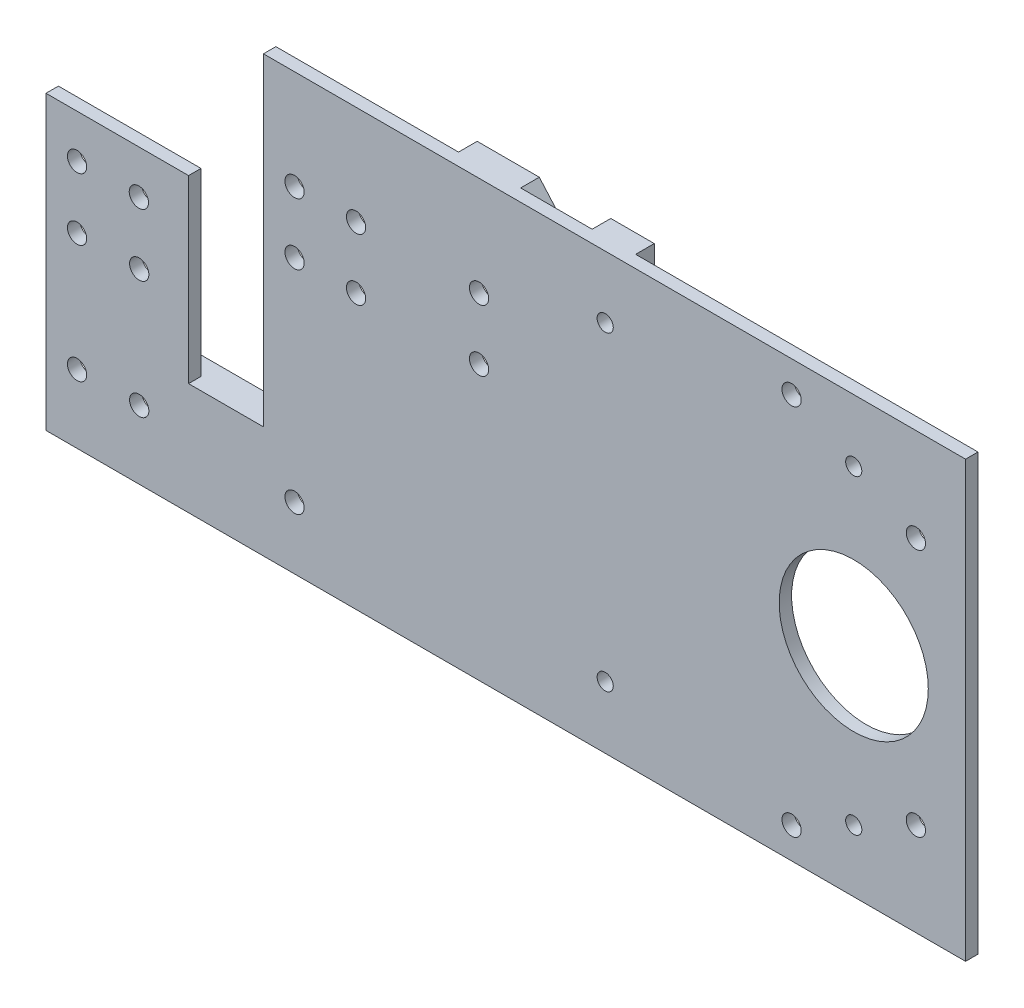
SolidWorks part; units mm, degrees
ref_plane "前视基准面" through (0, 0, 0) normal (0, 0, 1) x (1, 0, 0)
ref_plane "上视基准面" through (0, 0, 0) normal (0, 1, 0) x (1, 0, 0)
ref_plane "右视基准面" through (0, 0, 0) normal (1, 0, 0) x (0, 0, -1)
sketch "草图1" plane through (0, 0, 0) normal (0, 0, 1) x (1, 0, 0)
  line L0 (0, 0) -> (0, 35) construction
  line L1 (118, 35) -> (0, 35)
  line L2 (100, 0) -> (120, 0) construction
  line L3 (118, -35) -> (17.9, -35)
  line L4 (100, 0) -> (100, -25) construction
  line L5 (10, 9.1) -> (10, -25) construction
  line L6 (10, 19) -> (5, 19) construction
  line L7 (100, 0) -> (100, 25) construction
  line L8 (0, 0) -> (0, 19) construction
  line L9 (5, 19) -> (5, 35)
  line L10 (10, 19) -> (19.9, 19) construction
  line L11 (19.9, 19) -> (39.7, 19) construction
  line L12 (39.7, 19) -> (39.7, 9.1) construction
  line L13 (39.7, 9.1) -> (19.9, 9.1) construction
  line L14 (19.9, 9.1) -> (10, 9.1) construction
  line L15 (100, 0) -> (0, 0) construction
  line L16 (60, 0) -> (60, 25) construction
  line L17 (60, 0) -> (60, -25) construction
  line L18 (-15, 0) -> (-15, -5) construction
  line L19 (17.9, -35) -> (-7.0549, -35)
  line L20 (90, 0) -> (90, 30) construction
  line L21 (-15.0549, 19) -> (-15.0549, 4.9997) construction
  line L22 (90, 0) -> (90, -30) construction
  line L23 (90, 0) -> (110, 0) construction
  line L24 (110, 0) -> (110, 20) construction
  line L25 (110, 0) -> (110, -20) construction
  line L26 (-15, -5) -> (-15, -24) construction
  line L27 (-7.0549, -35) -> (-30, -35)
  line L28 (5, -17) -> (5, 19)
  line L29 (-15.0549, 4.9997) -> (-7.0549, 4.9997)
  line L30 (118, 35) -> (118, -35)
  line L31 (-30, -35) -> (-30, 11.9998)
  line L32 (-25, -5) -> (-25, -24) construction
  line L33 (-15.0549, 4.9997) -> (-15, 0) construction
  line L34 (-25, 5) -> (-25, 0) construction
  line L35 (-25, 0) -> (-25, -5) construction
  line L36 (-30, 11.9998) -> (-7.0549, 11.9998)
  line L37 (-7.0549, 11.9998) -> (-7.0549, -17)
  line L38 (-7.0549, -17) -> (5, -17)
  circle A0 centre (10, 19) radius 1.55
  circle A1 centre (19.9, 19) radius 1.55
  circle A2 centre (39.7, 19) radius 1.55
  circle A3 centre (39.7, 9.1) radius 1.55
  circle A4 centre (10, 9.1) radius 1.55
  circle A5 centre (19.9, 9.1) radius 1.55
  circle A6 centre (10, -25) radius 1.55
  circle A7 centre (-15, -24) radius 1.55
  circle A8 centre (90, 30) radius 1.55
  circle A9 centre (110, 20) radius 1.55
  circle A10 centre (90, -30) radius 1.55
  circle A11 centre (110, -20) radius 1.55
  circle A12 centre (-25, -24) radius 1.55
  circle A14 centre (60, 25) radius 1.3
  circle A15 centre (60, -25) radius 1.3
  circle A16 centre (-25, 5) radius 1.55
  circle A18 centre (100, 25) radius 1.3
  circle A19 centre (100, -25) radius 1.3
  circle A20 centre (100, 0) radius 12
  circle A21 centre (-15.0549, 4.9997) radius 1.55
  circle A22 centre (-15, -5) radius 1.55
  circle A23 centre (-25, -5) radius 1.55
extrude "凸台-拉伸1" add sketch "草图1" along normal blind 2
sketch "草图2" plane through (0, 0, 0) normal (0, 0, -1) x (-1, 0, 0)
  line L0 (30, -17) -> (-90, -17)
  line L1 (30, -35) -> (30, 11.9998) construction
  line L2 (-90, -17) -> (-90, -21)
  line L3 (-90, -21) -> (30, -21)
  line L4 (30, -21) -> (30, -17)
  line L5 (30, -35) -> (30, -30)
  line L6 (30, -30) -> (-80, -30)
  line L7 (-80, -30) -> (-80, -35)
  line L8 (-118, -35) -> (30, -35) construction
  line L9 (-80, -35) -> (30, -35)
  line L10 (-90, -17) -> (-80, -17)
  line L11 (-80, -17) -> (-34.3943, 35)
  line L12 (-118, 35) -> (-5, 35) construction
  line L13 (-34.3943, 35) -> (-44.3943, 35)
  line L14 (-44.3943, 35) -> (-90, -17)
  line L15 (-101.7073, 19.9018) -> (-101.7073, 13.9018)
  line L16 (-101.7073, 13.9018) -> (-62.8981, 13.9018)
  line L17 (-62.8981, 13.9018) -> (-57.6359, 19.9018)
  line L18 (-57.6359, 19.9018) -> (-101.7073, 19.9018)
  line L19 (-62.8981, 35) -> (-55.8981, 35)
  line L20 (-55.8981, 35) -> (-55.8981, 21.8833)
  line L21 (-55.8981, 21.8833) -> (-57.6359, 19.9018)
  line L22 (-62.8981, 35) -> (-62.8981, 19.9018)
  line L23 (-62.8981, 19.9018) -> (-57.6359, 19.9018)
  line L24 (-62.8981, 2.4997) -> (-62.8981, -17)
  line L25 (-62.8981, -17) -> (-57.1972, -17)
  line L26 (-57.1972, -17) -> (-57.1972, 9)
  line L27 (-57.1972, 9) -> (-62.8981, 2.4997)
  line L28 (-62.8981, -21) -> (-62.8981, -30)
  line L29 (-57.1972, -21) -> (-57.1972, -30)
  line L30 (-57.1972, -30) -> (-62.8981, -30)
  line L31 (-62.8981, -21) -> (-57.1972, -21)
  line M1 (7.0549, -17) -> (-5, -17)
  line M3 (-5, 35) -> (-118, 35)
  line M5 (-118, -35) -> (30, -35)
  line M6 (30, -35) -> (30, 11.9998)
  circle M16 centre (-60, -25) radius 1.3
  circle M17 centre (-60, 25) radius 1.3
extrude "凸台-拉伸2" add sketch "草图2" along normal blind 3 contours L14 L0 L11 M3 | L2 L3 L0 M6 M1 | L6 L7 M5 M6 | L14 L18 L15 L16 | L29 L3 L28 L6 M16 | L0 L26 L11 L24 | L22 L18 L14 L20 M3 M17
